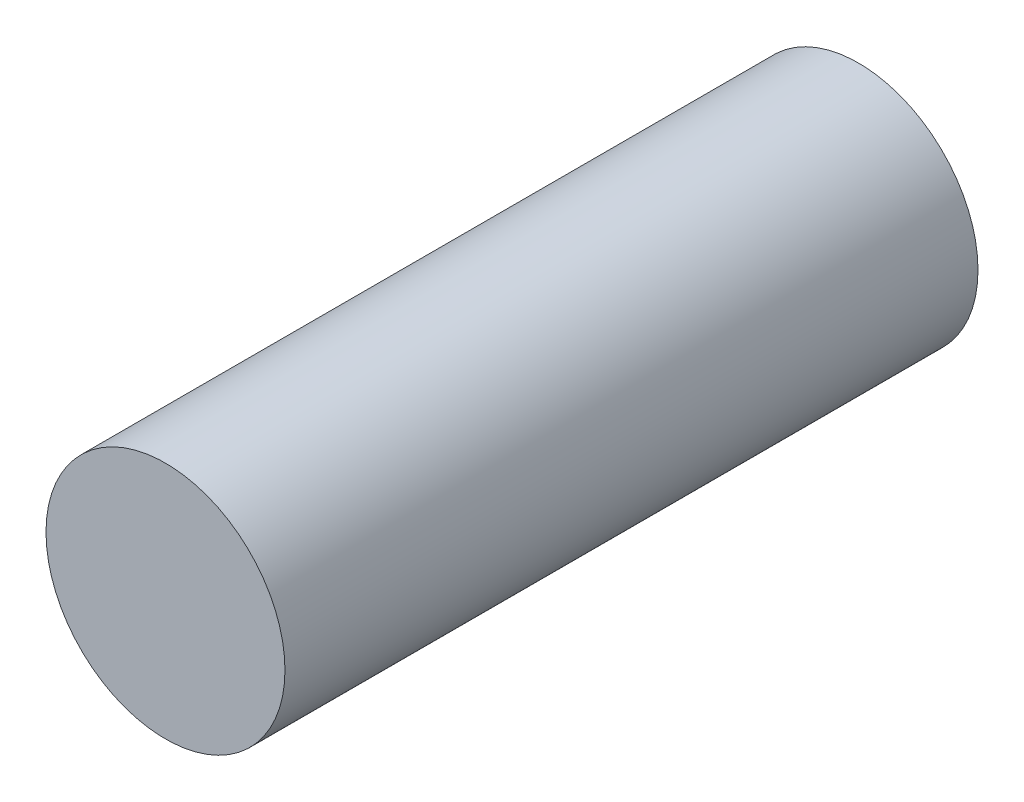
SolidWorks part; units mm, degrees
ref_plane "Front Plane" through (0, 0, 0) normal (0, 0, 1) x (1, 0, 0)
ref_plane "Top Plane" through (0, 0, 0) normal (0, 1, 0) x (1, 0, 0)
ref_plane "Right Plane" through (0, 0, 0) normal (1, 0, 0) x (0, 0, -1)
sketch "Sketch2" plane through (0, 0, 0) normal (0, 0, 1) x (1, 0, 0)
  circle A0 centre (0, 0) radius 5
  dimension "D1" = 10
extrude "Boss-Extrude1" add sketch "Sketch2" along normal blind 29
